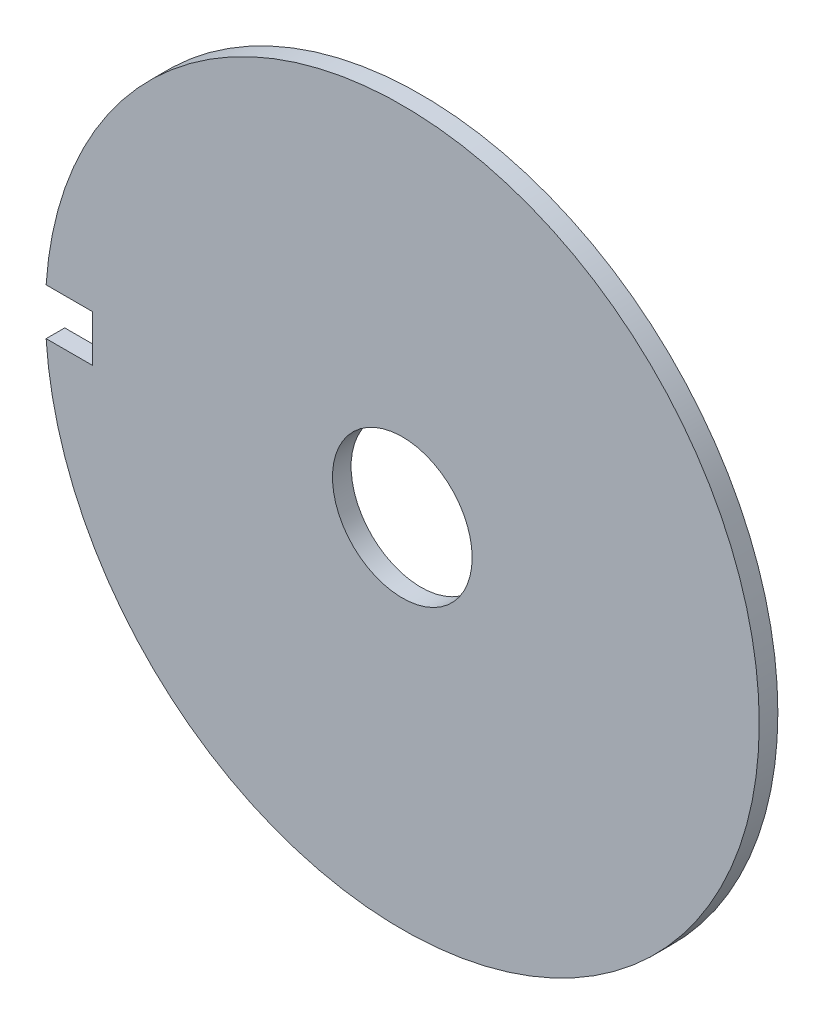
SolidWorks part; units mm, degrees
material "1.0037 (S235JR)"
ref_plane "Plan de face" through (0, 0, 0) normal (0, 0, 1) x (1, 0, 0)
ref_plane "Plan de dessus" through (0, 0, 0) normal (0, 1, 0) x (1, 0, 0)
ref_plane "Plan de droite" through (0, 0, 0) normal (1, 0, 0) x (0, 0, -1)
sketch "Esquisse1" plane through (0, 0, 0) normal (0, 0, 1) x (1, 0, 0)
  circle A0 centre (0, 0) radius 115
  circle A1 centre (0, 0) radius 22.5
  point P2 (0, 0)
  dimension "D1" = 230
  dimension "D4" = 45
extrude "Boss.-Extru.1" add sketch "Esquisse1" along normal blind 6 contours A0 | A1
sketch "Esquisse2" plane through (0, 0, 6) normal (0, 0, 1) x (1, 0, 0)
  line L0 (-114.7552, 7.5) -> (-99.7552, 7.5)
  line L1 (-99.7552, 7.5) -> (-99.7552, -7.5)
  line L2 (-99.7552, -7.5) -> (-114.7552, -7.5)
  line L3 (-114.7552, 7.5) -> (-126.6107, 0)
  line L4 (-126.6107, 0) -> (-114.7552, -7.5)
  line L5 (-99.7552, 0) -> (-126.6107, 0) construction
  circle A0 centre (0, 0) radius 115 construction
  dimension "D1" = 15
  dimension "D2" = 7.5
  dimension "D3" = 15
extrude "Enlèv. mat.-Extru.2" cut sketch "Esquisse2" against normal blind 6
